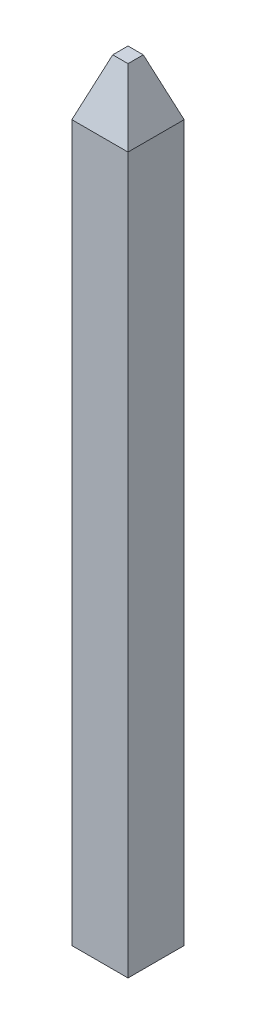
SolidWorks part; units mm, degrees
ref_plane "Front Plane" through (0, 0, 0) normal (0, 0, 1) x (1, 0, 0)
ref_plane "Top Plane" through (0, 0, 0) normal (0, 1, 0) x (1, 0, 0)
ref_plane "Right Plane" through (0, 0, 0) normal (1, 0, 0) x (0, 0, -1)
sketch "Sketch1" plane through (0, 0, 0) normal (0, 1, 0) x (1, 0, 0)
  line L1 (-0.25, -0.25) -> (0.25, -0.25)
  line L2 (-0.25, -0.25) -> (-0.25, 0.25)
  line L3 (-0.25, 0.25) -> (0.25, 0.25)
  line L4 (0.25, -0.25) -> (0.25, 0.25)
sketch "Sketch2" plane through (0, 0, 0) normal (0, 0, 1) x (1, 0, 0)
  line L0 (0, 0) -> (0, 6.37)
sweep "Sweep1" add profiles "Sketch1" path "Sketch2"
sketch "Sketch3" plane through (0, 6.37, 0) normal (0, 1, 0) x (1, 0, 0)
  line L1 (0.25, -0.25) -> (-0.25, -0.25)
  line L2 (0.25, -0.25) -> (0.25, 0.25)
  line L3 (0.25, 0.25) -> (-0.25, 0.25)
  line L4 (-0.25, -0.25) -> (-0.25, 0.25)
extrude "Boss-Extrude1" add sketch "Sketch3" along normal blind 0.5 draft 20
